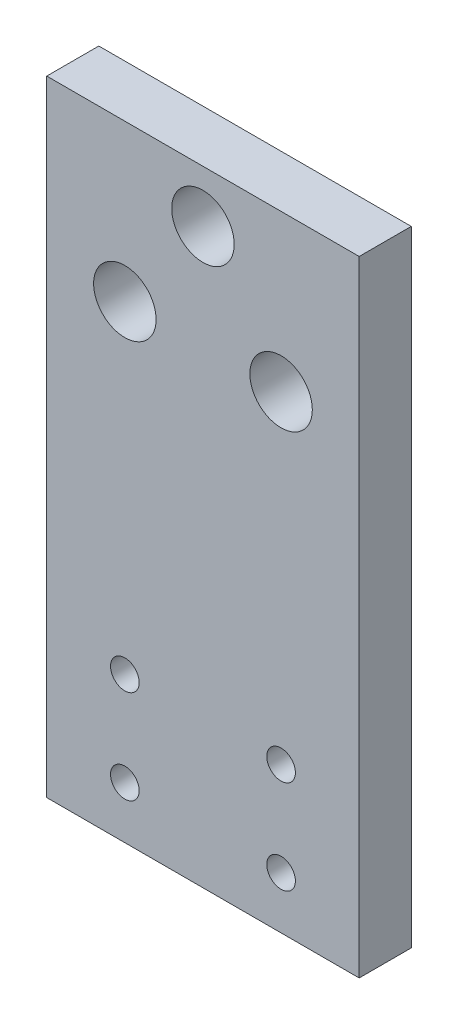
SolidWorks part; units mm, degrees
ref_plane "前视基准面" through (0, 0, 0) normal (0, 0, 1) x (1, 0, 0)
ref_plane "上视基准面" through (0, 0, 0) normal (0, 1, 0) x (1, 0, 0)
ref_plane "右视基准面" through (0, 0, 0) normal (1, 0, 0) x (0, 0, -1)
sketch "草图1" plane through (0, 0, 0) normal (0, 0, 1) x (1, 0, 0)
  line L1 (-30, 60) -> (30, 60)
  line L2 (-30, 60) -> (-30, -60)
  line L3 (-30, -60) -> (30, -60)
  line L4 (30, 60) -> (30, -60)
  line L5 (-30, 60) -> (30, -60) construction
  line L6 (-30, -60) -> (30, 60) construction
  point P0 (0, 0)
  dimension "D1" = 60
  dimension "D2" = 120
extrude "凸台-拉伸1" add sketch "草图1" along normal blind 10
sketch "草图2" plane through (0, 0, 10) normal (0, 0, 1) x (1, 0, 0)
  line L0 (0, 0) -> (0, -70.6909) construction
  line L1 (-15, -32) -> (15, -32)
  line L2 (-15, -32) -> (-15, -50)
  line L3 (-15, -50) -> (15, -50)
  line L4 (15, -32) -> (15, -50)
  line L5 (-15, -32) -> (15, -50) construction
  line L6 (-15, -50) -> (15, -32) construction
  line L7 (-30, -60) -> (30, -60) construction
  line L8 (-15, 30) -> (15, 30)
  line L9 (0, 30) -> (0, 50)
  line L10 (30, 60) -> (-30, 60) construction
  point P0 (0, -41)
  dimension "D1" = 10
  dimension "D2" = 18
  dimension "D3" = 30
  dimension "D4" = 30
  dimension "D5" = 20
  dimension "D6" = 30
hole_wizard "大小mm 暗销孔1" positions "3D草图1" profile "草图3" hole size "Ø8.0" standard "GB"
sketch3d "3D草图1"
  point P0 (-15, -32, 10)
  point P3 (15, -32, 10)
  point P6 (15, -50, 10)
  point P9 (-15, -50, 10)
sketch "草图3" plane through (-15, -32, 10) normal (1, 0, 0) x (0, -1, 0)
  line L0 (0, 0) -> (0, 16.6524)
  line L1 (0, 16.6524) -> (2.75, 15)
  line L2 (2.75, 15) -> (2.75, 0)
  line L5 (2.75, 0) -> (0, 0)
  line L10 (0, 16.6524) -> (-2.75, 15) construction
  line L11 (0, -6.35) -> (0, 107.95) construction
  dimension "孔直径" = 5.5
  dimension "孔深度" = 15
  dimension "导头角度" = 118
hole_wizard "大小mm 暗销槽口1" positions "草图4" profile "草图5" size "Ø12.0" standard "GB" slot yes
sketch "草图4" plane through (0, 0, 10) normal (0, 0, 1) x (1, 0, 0)
  point P0 (-15, 30)
  point P3 (15, 30)
  point P6 (0, 50)
sketch "草图5" plane through (-15, 30, 10) normal (1, 0, 0) x (0, -1, 0)
  line L0 (0, 0) -> (0, 18.6052)
  line L1 (0, 18.6052) -> (6, 15)
  line L2 (6, 15) -> (6, 0)
  line L5 (6, 0) -> (0, 0)
  line L10 (0, 18.6052) -> (-6, 15) construction
  line L11 (0, -6.35) -> (0, 107.95) construction
  dimension "孔直径" = 12
  dimension "孔深度" = 15
  dimension "导头角度" = 118
